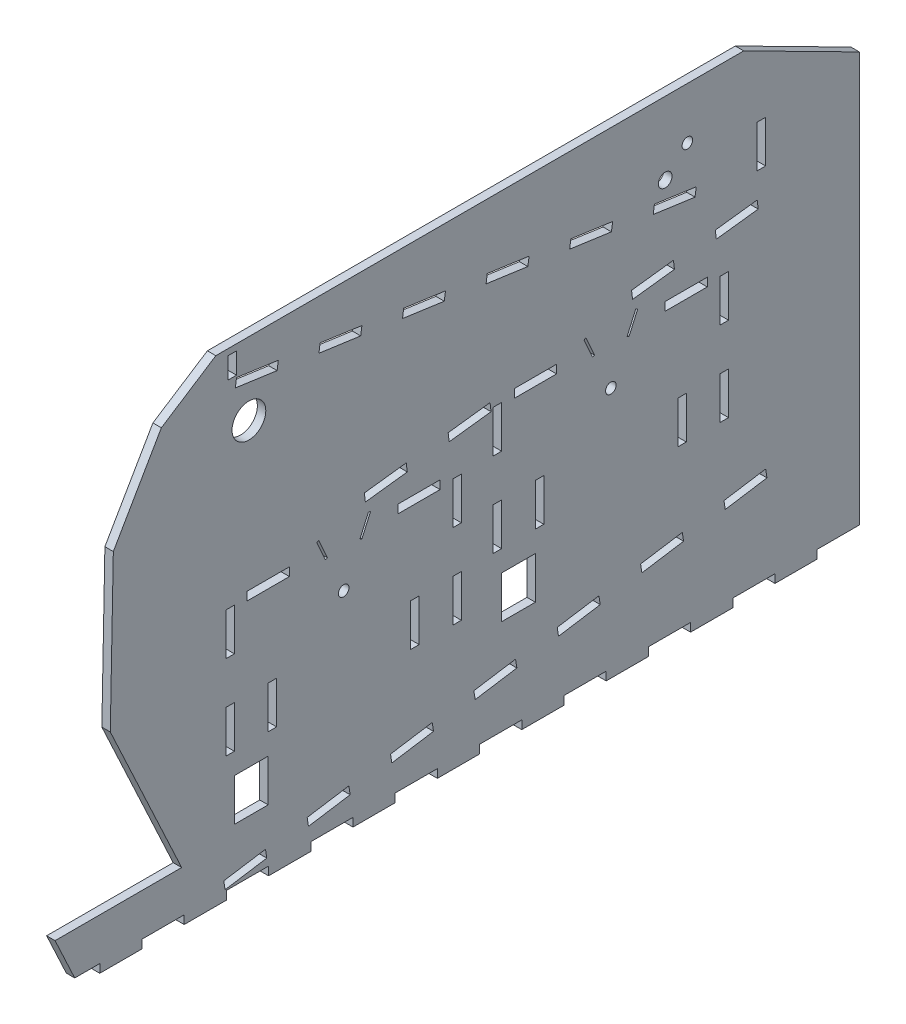
SolidWorks part; units mm, degrees
ref_plane "Спереди" through (0, 0, 0) normal (0, 0, 1) x (1, 0, 0)
ref_plane "Сверху" through (0, 0, 0) normal (0, 1, 0) x (1, 0, 0)
ref_plane "Справа" through (0, 0, 0) normal (1, 0, 0) x (0, 0, -1)
sketch "Эскиз1" plane through (0, 0, 0) normal (1, 0, 0) x (0, 0, -1)
  line L0 (0, 0) -> (-31.7705, 0) construction
  line L1 (0, 0) -> (-25.7029, 18.6742) construction
  line L2 (0, 0) -> (-25.7029, 18.6742) construction
  line L3 (0, 0) -> (-9.8176, 30.2156) construction
  line L4 (0, 0) -> (-9.8176, 30.2156) construction
  line L5 (0, 0) -> (9.8176, 30.2156) construction
  line L6 (0, 0) -> (9.8176, 30.2156) construction
  line L7 (0, 0) -> (25.7029, 18.6742) construction
  line L8 (0, 0) -> (25.7029, 18.6742) construction
  line L9 (0, 0) -> (31.7705, 0) construction
  line L10 (-31.7705, 0) -> (-31.7705, -31.7705) construction
  line L11 (-25.7029, 18.6742) -> (-51.7705, 18.6742) construction
  line L12 (-51.7705, 18.6742) -> (-51.7705, -31.7705) construction
  line L13 (0, 0) -> (0, -37.2268) construction
  line L14 (25.7029, 18.6742) -> (51.7705, 18.6742) construction
  line L15 (51.7705, 18.6742) -> (51.7705, -31.7705) construction
  line L16 (31.7705, 0) -> (31.7705, -31.7705) construction
  line L17 (10.3051, 31.2454) -> (28.3345, 31.2454) construction
  line L18 (9.8176, 35.2156) -> (10.3051, 31.2454) construction
  line L19 (9.8176, 35.2156) -> (69.3704, 42.5277) construction
  line L20 (10.3051, 31.2454) -> (69.8579, 38.5575) construction
  line L21 (25.7029, 18.6742) -> (25.7029, 22.6742) construction
  line L22 (25.7029, 22.6742) -> (55.7705, 22.6742) construction
  line L23 (55.7705, 22.6742) -> (55.7705, -31.7705) construction
  line L24 (55.7705, -31.7705) -> (51.7705, -31.7705) construction
  line L25 (31.7705, 0) -> (35.7705, 0) construction
  line L26 (35.7705, 0) -> (35.7705, -31.7705) construction
  line L27 (35.7705, -31.7705) -> (31.7705, -31.7705) construction
  line L28 (-31.7705, 0) -> (-35.7705, 0) construction
  line L29 (-35.7705, 0) -> (-35.7705, -31.7705) construction
  line L30 (-35.7705, -31.7705) -> (-31.7705, -31.7705) construction
  line L31 (-31.7705, -31.7705) -> (-32.0988, -31.7383) construction
  line L32 (-25.7029, 18.6742) -> (-25.7029, 22.6742) construction
  line L33 (-25.7029, 22.6742) -> (-55.7705, 22.6742) construction
  line L34 (-55.7705, 22.6742) -> (-55.7705, -31.7705) construction
  line L35 (-55.7705, -31.7705) -> (-51.7705, -31.7705) construction
  line L36 (69.3704, 42.5277) -> (69.8579, 38.5575) construction
  line L37 (9.8176, 30.2156) -> (9.8176, 40.2156)
  line L38 (51.7705, 18.6742) -> (55.7705, 18.6742) construction
  line L39 (126.6284, 19.8535) -> (94.8579, 19.8535) construction
  line L40 (126.6284, 19.8535) -> (100.9255, 38.5277) construction
  line L41 (126.6284, 19.8535) -> (100.9255, 38.5277) construction
  line L42 (126.6284, 19.8535) -> (116.8108, 50.069) construction
  line L43 (126.6284, 19.8535) -> (116.8108, 50.069) construction
  line L44 (126.6284, 19.8535) -> (136.446, 50.069) construction
  line L45 (199.9988, -50.0348) -> (180.2402, -53.1327)
  line L46 (126.6284, 19.8535) -> (136.446, 50.069) construction
  line L47 (126.6284, 19.8535) -> (152.3313, 38.5277) construction
  line L48 (126.6284, 19.8535) -> (152.3313, 38.5277) construction
  line L49 (126.6284, 19.8535) -> (158.3989, 19.8535) construction
  line L50 (94.8579, 19.8535) -> (94.8579, -11.917) construction
  line L51 (100.9255, 38.5277) -> (74.8579, 38.5277) construction
  line L52 (74.8579, 38.5277) -> (74.8579, -11.917) construction
  line L53 (126.6284, 19.8535) -> (126.6284, -17.4484) construction
  line L54 (152.3313, 38.5277) -> (178.3989, 38.5277) construction
  line L55 (178.3989, 38.5277) -> (178.3989, -11.917) construction
  line L56 (158.3989, 19.8535) -> (158.3989, -11.917) construction
  line L57 (136.9335, 51.0988) -> (174.1594, 51.0988) construction
  line L58 (136.446, 55.069) -> (136.9335, 51.0988) construction
  line L59 (136.446, 55.069) -> (195.9988, 62.3812) construction
  line L60 (136.9335, 51.0988) -> (196.4863, 58.411) construction
  line L61 (152.3313, 38.5277) -> (152.3313, 42.5277) construction
  line L62 (152.3313, 42.5277) -> (182.3989, 42.5277) construction
  line L63 (182.3989, 42.5277) -> (182.3989, -11.917) construction
  line L64 (182.3989, -11.917) -> (178.3989, -11.917) construction
  line L65 (158.3989, 19.8535) -> (162.3989, 19.8535) construction
  line L66 (69.3704, 42.5277) -> (69.8579, 38.5575)
  line L67 (69.3704, 42.5277) -> (49.5195, 40.0903)
  line L68 (69.8579, 38.5575) -> (50.007, 36.1201)
  line L69 (49.5195, 40.0903) -> (50.007, 36.1201)
  line L70 (29.6686, 37.6529) -> (9.8176, 35.2156)
  line L71 (9.8176, 35.2156) -> (10.3051, 31.2454)
  line L72 (30.156, 33.6828) -> (10.3051, 31.2454)
  line L73 (29.6686, 37.6529) -> (30.156, 33.6828)
  line L74 (162.3989, 19.8535) -> (162.3989, -11.917) construction
  line L75 (25.7029, 18.6742) -> (45.7029, 18.6742)
  line L76 (25.7029, 18.6742) -> (25.7029, 22.6742)
  line L77 (25.7029, 22.6742) -> (45.7029, 22.6742)
  line L78 (45.7029, 18.6742) -> (45.7029, 22.6742)
  line L79 (51.7705, 20) -> (55.7705, 20)
  line L80 (51.7705, 20) -> (51.7705, 0)
  line L81 (51.7705, 0) -> (55.7705, 0)
  line L82 (55.7705, 20) -> (55.7705, 0)
  line L83 (-31.7705, -20) -> (-35.7705, -20)
  line L84 (-31.7705, -20) -> (-31.7705, -40)
  line L85 (-31.7705, -40) -> (-35.7705, -40)
  line L86 (-25.7029, 18.6742) -> (-45.7029, 18.6742)
  line L87 (-25.7029, 18.6742) -> (-25.7029, 22.6742)
  line L88 (-25.7029, 22.6742) -> (-45.7029, 22.6742)
  line L89 (-45.7029, 18.6742) -> (-45.7029, 22.6742)
  line L90 (-35.7705, -20) -> (-35.7705, -40)
  line L91 (31.7705, -20) -> (35.7705, -20)
  line L92 (31.7705, -20) -> (31.7705, -40)
  line L93 (31.7705, -40) -> (35.7705, -40)
  line L94 (-55.7705, 20) -> (-51.7705, 20)
  line L95 (-55.7705, 20) -> (-55.7705, 0)
  line L96 (-55.7705, 0) -> (-51.7705, 0)
  line L97 (-51.7705, 20) -> (-51.7705, 0)
  line L98 (162.3989, -11.917) -> (158.3989, -11.917) construction
  line L99 (94.8579, 19.8535) -> (90.8579, 19.8535) construction
  line L100 (90.8579, 19.8535) -> (90.8579, -11.917) construction
  line L101 (90.8579, -11.917) -> (94.8579, -11.917) construction
  line L102 (179.9988, 80.4295) -> (130.5186, 80.4295) construction
  line L103 (100.9255, 38.5277) -> (100.9255, 42.5277) construction
  line L104 (100.9255, 42.5277) -> (70.8579, 42.5277) construction
  line L105 (70.8579, 42.5277) -> (70.8579, -11.917) construction
  line L106 (70.8579, -11.917) -> (74.8579, -11.917) construction
  line L107 (195.9988, 62.3812) -> (196.4863, 58.411) construction
  line L108 (136.446, 50.069) -> (136.446, 60.069)
  line L109 (178.3989, 38.5277) -> (182.3989, 38.5277) construction
  line L110 (179.9988, 80.4295) -> (179.4421, 76.4684) construction
  line L111 (195.9988, 62.3812) -> (196.4863, 58.411)
  line L112 (195.9988, 62.3812) -> (176.1479, 59.9438)
  line L113 (35.7705, -20) -> (35.7705, -40)
  line L114 (196.4863, 58.411) -> (176.6353, 55.9736)
  line L115 (176.1479, 59.9438) -> (176.6353, 55.9736)
  line L116 (156.2969, 57.5064) -> (136.446, 55.069)
  line L117 (136.446, 55.069) -> (136.9335, 51.0988)
  line L118 (156.7844, 53.5362) -> (136.9335, 51.0988)
  line L119 (156.2969, 57.5064) -> (156.7844, 53.5362)
  line L120 (152.3313, 38.5277) -> (172.3313, 38.5277)
  line L121 (152.3313, 38.5277) -> (152.3313, 42.5277)
  line L122 (152.3313, 42.5277) -> (172.3313, 42.5277)
  line L123 (172.3313, 38.5277) -> (172.3313, 42.5277)
  line L124 (178.3989, 19.8535) -> (182.3989, 19.8535)
  line L125 (178.3989, 19.8535) -> (178.3989, 39.8535)
  line L126 (178.3989, 39.8535) -> (182.3989, 39.8535)
  line L127 (182.3989, 19.8535) -> (182.3989, 39.8535)
  line L128 (94.8579, -0.1465) -> (90.8579, -0.1465)
  line L129 (94.8579, -0.1465) -> (94.8579, -20.1465)
  line L130 (94.8579, -20.1465) -> (90.8579, -20.1465)
  line L131 (100.9255, 38.5277) -> (80.9255, 38.5277)
  line L132 (100.9255, 38.5277) -> (100.9255, 42.5277)
  line L133 (100.9255, 42.5277) -> (80.9255, 42.5277)
  line L134 (80.9255, 38.5277) -> (80.9255, 42.5277)
  line L135 (90.8579, -0.1465) -> (90.8579, -20.1465)
  line L136 (158.3989, -0.1465) -> (162.3989, -0.1465)
  line L137 (158.3989, -0.1465) -> (158.3989, -20.1465)
  line L138 (158.3989, -20.1465) -> (162.3989, -20.1465)
  line L139 (70.8579, 39.8535) -> (74.8579, 39.8535)
  line L140 (70.8579, 39.8535) -> (70.8579, 19.8535)
  line L141 (70.8579, 19.8535) -> (74.8579, 19.8535)
  line L142 (74.8579, 39.8535) -> (74.8579, 19.8535)
  line L143 (162.3989, -0.1465) -> (162.3989, -20.1465)
  line L144 (179.9988, 80.4295) -> (-50.7705, 112.862) construction
  line L145 (-50.7705, 112.862) -> (-50.7705, 126.7706) construction
  line L146 (195.9988, 62.3812) -> (195.9988, 94.3381) construction
  line L147 (-76.7705, -75.2294) -> (-128.8786, 36.5168)
  line L148 (195.9988, 94.3381) -> (-34.7705, 126.7706) construction
  line L149 (-34.7705, 126.7706) -> (244.4209, 126.7706)
  line L150 (-51.7705, -40) -> (-51.7705, -50) construction
  line L151 (162.8814, 102.3387) -> (147.4568, 90.7154) construction
  line L152 (162.8814, 102.3387) -> (174.5046, 86.9141) construction
  line L153 (162.8814, 102.3387) -> (182.0071, 99.6508) construction
  line L154 (162.8814, 102.3387) -> (160.1934, 83.213) construction
  line L155 (-55.7705, -20) -> (-51.7705, -20)
  line L156 (-55.7705, -20) -> (-55.7705, -40)
  line L157 (-55.7705, -40) -> (-51.7705, -40)
  line L158 (-51.7705, -20) -> (-51.7705, -40)
  line L159 (74.8579, -20.1465) -> (74.8579, -50.1465) construction
  line L160 (-51.7705, -50) -> (-35.7705, -50)
  line L161 (-51.7705, -50) -> (-51.7705, -70)
  line L162 (-51.7705, -70) -> (-35.7705, -70)
  line L163 (-35.7705, -50) -> (-35.7705, -70)
  line L164 (70.8579, -0.1465) -> (74.8579, -0.1465)
  line L165 (70.8579, -0.1465) -> (70.8579, -20.1465)
  line L166 (70.8579, -20.1465) -> (74.8579, -20.1465)
  line L167 (74.8579, -0.1465) -> (74.8579, -20.1465)
  line L168 (-132.357, -75.2294) -> (-123.0308, -95.2294) construction
  line L169 (74.8579, -50.1465) -> (90.8579, -50.1465)
  line L170 (74.8579, -50.1465) -> (74.8579, -30.1465)
  line L171 (74.8579, -30.1465) -> (90.8579, -30.1465)
  line L172 (90.8579, -50.1465) -> (90.8579, -30.1465)
  line L173 (51.7705, -20) -> (55.7705, -20)
  line L174 (51.7705, -20) -> (51.7705, -40)
  line L175 (51.7705, -40) -> (55.7705, -40)
  line L176 (55.7705, -20) -> (55.7705, -40)
  line L177 (178.3989, -0.1465) -> (182.3989, -0.1465)
  line L178 (178.3989, -0.1465) -> (178.3989, -20.1465)
  line L179 (178.3989, -20.1465) -> (182.3989, -20.1465)
  line L180 (182.3989, -0.1465) -> (182.3989, -20.1465)
  line L181 (-88.2588, -95.2294) -> (199.9988, -50.0348) construction
  line L182 (-123.0308, -95.2294) -> (-88.2588, -95.2294) construction
  line L183 (-132.357, -75.2294) -> (-136.7705, -75.2294) construction
  line L184 (-76.7705, -75.2294) -> (-136.7705, -75.2294)
  line L185 (-136.7705, -75.2294) -> (-125.5791, -99.2294)
  line L186 (-125.5791, -99.2294) -> (244.4209, -99.2294)
  line L187 (244.4209, -99.2294) -> (244.4209, 126.7706)
  line L188 (-128.8786, 36.5168) -> (-76.7705, 126.7706)
  line L189 (-76.7705, 126.7706) -> (-34.7705, 126.7706)
  line L190 (-50.7705, 112.862) -> (-30.9651, 110.0786)
  line L191 (204.4209, -99.2294) -> (184.4209, -99.2294)
  line L192 (-50.7705, 113.862) -> (-54.7705, 113.862)
  line L193 (-50.7705, 113.862) -> (-50.7705, 123.862)
  line L194 (-50.7705, 123.862) -> (-54.7705, 123.862)
  line L195 (-50.7705, 112.862) -> (-51.3272, 108.9009)
  line L196 (-30.9651, 110.0786) -> (-31.5218, 106.1175)
  line L197 (-51.3272, 108.9009) -> (-31.5218, 106.1175)
  line L198 (-11.1598, 107.2951) -> (-11.7165, 103.334)
  line L199 (-11.7165, 103.334) -> (8.0889, 100.5506)
  line L200 (8.6456, 104.5116) -> (8.0889, 100.5506)
  line L201 (-11.1598, 107.2951) -> (8.6456, 104.5116)
  line L202 (28.4509, 101.7282) -> (27.8942, 97.7671)
  line L203 (27.8942, 97.7671) -> (47.6996, 94.9836)
  line L204 (48.2563, 98.9447) -> (47.6996, 94.9836)
  line L205 (28.4509, 101.7282) -> (48.2563, 98.9447)
  line L206 (68.0617, 96.1612) -> (67.505, 92.2002)
  line L207 (67.505, 92.2002) -> (87.3103, 89.4167)
  line L208 (87.867, 93.3778) -> (87.3103, 89.4167)
  line L209 (68.0617, 96.1612) -> (87.867, 93.3778)
  line L210 (107.6724, 90.5943) -> (107.1157, 86.6332)
  line L211 (107.1157, 86.6332) -> (126.9211, 83.8498)
  line L212 (127.4777, 87.8109) -> (126.9211, 83.8498)
  line L213 (107.6724, 90.5943) -> (127.4777, 87.8109)
  line L214 (147.2831, 85.0274) -> (146.7264, 81.0663)
  line L215 (146.7264, 81.0663) -> (166.5318, 78.2829)
  line L216 (167.0885, 82.2439) -> (166.5318, 78.2829)
  line L217 (147.2831, 85.0274) -> (167.0885, 82.2439)
  line L218 (179.9988, 80.4295) -> (175.1542, 81.1104) construction
  line L219 (179.4421, 76.4684) -> (174.5975, 77.1493) construction
  line L220 (175.1542, 81.1104) -> (174.5975, 77.1493) construction
  line L221 (195.9988, 94.3381) -> (199.9988, 94.3381)
  line L222 (195.9988, 94.3381) -> (195.9988, 74.3381)
  line L223 (195.9988, 74.3381) -> (199.9988, 74.3381)
  line L224 (199.9988, 94.3381) -> (199.9988, 74.3381)
  line L225 (199.9988, -50.0348) -> (200.6184, -53.9866)
  line L226 (180.2402, -53.1327) -> (180.8597, -57.0844)
  line L227 (200.6184, -53.9866) -> (180.8597, -57.0844)
  line L228 (160.4912, -56.2922) -> (140.7326, -59.3901)
  line L229 (160.4912, -56.2922) -> (161.1108, -60.2439)
  line L230 (140.7326, -59.3901) -> (141.3522, -63.3418)
  line L231 (161.1108, -60.2439) -> (141.3522, -63.3418)
  line L232 (120.9837, -62.5496) -> (101.2251, -65.6475)
  line L233 (120.9837, -62.5496) -> (121.6033, -66.5013)
  line L234 (101.2251, -65.6475) -> (101.8447, -69.5992)
  line L235 (121.6033, -66.5013) -> (101.8447, -69.5992)
  line L236 (81.4762, -68.807) -> (61.7176, -71.9048)
  line L237 (81.4762, -68.807) -> (82.0958, -72.7587)
  line L238 (61.7176, -71.9048) -> (62.3371, -75.8566)
  line L239 (82.0958, -72.7587) -> (62.3371, -75.8566)
  line L240 (41.9686, -75.0643) -> (22.21, -78.1622)
  line L241 (41.9686, -75.0643) -> (42.5882, -79.0161)
  line L242 (22.21, -78.1622) -> (22.8296, -82.1139)
  line L243 (42.5882, -79.0161) -> (22.8296, -82.1139)
  line L244 (2.4611, -81.3217) -> (-17.2975, -84.4196)
  line L245 (2.4611, -81.3217) -> (3.0807, -85.2735)
  line L246 (-17.2975, -84.4196) -> (-16.6779, -88.3713)
  line L247 (3.0807, -85.2735) -> (-16.6779, -88.3713)
  line L248 (-54.7705, 113.862) -> (-54.7705, 123.862)
  line L249 (244.4209, -99.2294) -> (224.4209, -99.2294)
  line L250 (244.4209, -99.2294) -> (244.4209, -95.2294)
  line L251 (244.4209, -95.2294) -> (224.4209, -95.2294)
  line L252 (224.4209, -99.2294) -> (224.4209, -95.2294)
  line L253 (204.4209, -99.2294) -> (204.4209, -95.2294)
  line L254 (204.4209, -95.2294) -> (184.4209, -95.2294)
  line L255 (184.4209, -99.2294) -> (184.4209, -95.2294)
  line L256 (164.4209, -99.2294) -> (144.4209, -99.2294)
  line L257 (164.4209, -99.2294) -> (164.4209, -95.2294)
  line L258 (164.4209, -95.2294) -> (144.4209, -95.2294)
  line L259 (144.4209, -99.2294) -> (144.4209, -95.2294)
  line L260 (124.4209, -99.2294) -> (104.4209, -99.2294)
  line L261 (124.4209, -99.2294) -> (124.4209, -95.2294)
  line L262 (124.4209, -95.2294) -> (104.4209, -95.2294)
  line L263 (104.4209, -99.2294) -> (104.4209, -95.2294)
  line L264 (84.4209, -99.2294) -> (64.4209, -99.2294)
  line L265 (84.4209, -99.2294) -> (84.4209, -95.2294)
  line L266 (84.4209, -95.2294) -> (64.4209, -95.2294)
  line L267 (64.4209, -99.2294) -> (64.4209, -95.2294)
  line L268 (44.4209, -99.2294) -> (24.4209, -99.2294)
  line L269 (44.4209, -99.2294) -> (44.4209, -95.2294)
  line L270 (44.4209, -95.2294) -> (24.4209, -95.2294)
  line L271 (24.4209, -99.2294) -> (24.4209, -95.2294)
  line L272 (4.4209, -99.2294) -> (-15.5791, -99.2294)
  line L273 (4.4209, -99.2294) -> (4.4209, -95.2294)
  line L274 (4.4209, -95.2294) -> (-15.5791, -95.2294)
  line L275 (-15.5791, -99.2294) -> (-15.5791, -95.2294)
  line L276 (-35.5791, -99.2294) -> (-55.5791, -99.2294)
  line L277 (-35.5791, -99.2294) -> (-35.5791, -95.2294)
  line L278 (-35.5791, -95.2294) -> (-55.5791, -95.2294)
  line L279 (-55.5791, -99.2294) -> (-55.5791, -95.2294)
  line L280 (-75.5791, -99.2294) -> (-95.5791, -99.2294)
  line L281 (-75.5791, -99.2294) -> (-75.5791, -95.2294)
  line L282 (-75.5791, -95.2294) -> (-95.5791, -95.2294)
  line L283 (-95.5791, -99.2294) -> (-95.5791, -95.2294)
  line L284 (-115.5791, -99.2294) -> (-135.5791, -99.2294)
  line L285 (-115.5791, -99.2294) -> (-115.5791, -95.2294)
  line L286 (-115.5791, -95.2294) -> (-135.5791, -95.2294)
  line L287 (-135.5791, -99.2294) -> (-135.5791, -95.2294)
  line L288 (-110.6007, -2.6803) -> (-109.1606, 70.6694)
  line L289 (-37.0464, -87.5791) -> (-56.805, -90.677)
  line L290 (-37.0464, -87.5791) -> (-36.4268, -91.5308)
  line L291 (-56.805, -90.677) -> (-56.1855, -94.6287)
  line L292 (-36.4268, -91.5308) -> (-56.1855, -94.6287)
  line L293 (-86.4077, 110.0786) -> (-60.5791, 126.7706)
  line L294 (189.6222, 126.7706) -> (244.4209, 98.9447)
  line L295 (-12.7089, 26.0861) -> (-8.6415, 16.9506)
  line L296 (-12.7089, 26.0861) -> (-11.7954, 26.4928)
  line L297 (-8.6415, 16.9506) -> (-7.728, 17.3574)
  line L298 (-11.7954, 26.4928) -> (-7.728, 17.3574)
  line L299 (8.6415, 16.9506) -> (7.728, 17.3574)
  line L300 (11.7954, 26.4928) -> (7.728, 17.3574)
  line L301 (12.7089, 26.0861) -> (8.6415, 16.9506)
  line L302 (12.7089, 26.0861) -> (11.7954, 26.4928)
  line L303 (114.833, 46.3463) -> (118.9004, 37.2108)
  line L304 (114.833, 46.3463) -> (113.9195, 45.9396)
  line L305 (118.9004, 37.2108) -> (117.9868, 36.8041)
  line L306 (113.9195, 45.9396) -> (117.9868, 36.8041)
  line L307 (134.3564, 37.2108) -> (135.2699, 36.8041)
  line L308 (139.3373, 45.9396) -> (135.2699, 36.8041)
  line L309 (138.4237, 46.3463) -> (134.3564, 37.2108)
  line L310 (138.4237, 46.3463) -> (139.3373, 45.9396)
  line L311 (161.3068, 91.1351) -> (116.07, 97.4927) construction
  circle A0 centre (0, 0) radius 31.7705 construction
  circle A1 centre (-23.0826, 7.5) radius 7.5 construction
  circle A2 centre (-14.2658, 19.6353) radius 7.5 construction
  circle A3 centre (0, 24.2705) radius 7.5 construction
  circle A4 centre (14.2658, 19.6353) radius 7.5 construction
  circle A5 centre (23.0826, 7.5) radius 7.5 construction
  circle A6 centre (0, 0) radius 2.5
  circle A7 centre (126.6284, 19.8535) radius 31.7705 construction
  circle A8 centre (103.5458, 27.3535) radius 7.5 construction
  circle A9 centre (112.3625, 39.4887) radius 7.5 construction
  circle A10 centre (126.6284, 44.124) radius 7.5 construction
  circle A11 centre (140.8942, 39.4887) radius 7.5 construction
  circle A12 centre (149.711, 27.3535) radius 7.5 construction
  circle A13 centre (126.6284, 19.8535) radius 2.5
  circle A14 centre (162.8814, 102.3387) radius 19.3137 construction
  circle A15 centre (161.3068, 91.1351) radius 8 construction
  arc A16 (177.7354, 100.2511) -> (170.529, 120.0738) centre (158.1612, 104.3563) ccw construction
  circle A17 centre (162.8814, 102.3387) radius 2.5
  circle A18 centre (169.6901, 93.3032) radius 8 construction
  circle A19 centre (152.3944, 92.3877) radius 3.25
  point P6 (0, 31.7705)
  point P55 (126.6284, 51.624)
  point P192 (-35.7705, -87)
  point P194 (90.8579, -67.1465)
  dimension "D1" = 15
  dimension "D20" = 5
  dimension "D7" = 15
  dimension "D35" = 5
  dimension "D50" = 20
  dimension "D51" = 5
  dimension "D52" = 16
  dimension "D85" = 6.5
  dimension "D2" = 36
  dimension "D3" = 16
  dimension "D4" = 16
  dimension "D5" = 60
  dimension "D8" = 36
  dimension "D9" = 16
  dimension "D10" = 16
  dimension "D11" = 4
  dimension "D12" = 60
  dimension "D13" = 20
  dimension "D14" = 20
  dimension "D15" = 20
  dimension "D16" = 20
  dimension "D17" = 20
  dimension "D18" = 30
  dimension "D19" = 20
  dimension "D21" = 4
  dimension "D22" = 20
  dimension "D23" = 20
  dimension "D24" = 20
  dimension "D25" = 4
  dimension "D26" = 20
  dimension "D27" = 7
  dimension "D28" = 5
  dimension "D29" = 20
  dimension "D30" = 20
  dimension "D31" = 17
  dimension "D32" = 20
  dimension "D33" = 30
  dimension "D34" = 20
  dimension "D36" = 20
  dimension "D37" = 20
  dimension "D38" = 4
  dimension "D39" = 20
  dimension "D40" = 7
  dimension "D41" = 5
  dimension "D42" = 16
  dimension "D43" = 16
  dimension "D44" = 26
  dimension "D45" = 4
  dimension "D46" = 45
  dimension "D47" = 16
  dimension "D48" = 4
  dimension "D49" = 15
  dimension "D53" = 20
  dimension "D54" = 20
  dimension "D55" = 20
  dimension "D56" = 17
  dimension "D57" = 125
  dimension "D58" = 21
  dimension "D59" = 60
  dimension "D60" = 226
  dimension "D61" = 8
  dimension "D62" = 16
  dimension "D63" = 120
  dimension "D64" = 370
  dimension "D65" = 10
  dimension "D66" = 1
  dimension "D67" = 20
  dimension "D69" = 20
  dimension "D70" = 20
  dimension "D71" = 4
  dimension "D73" = 4
  dimension "D74" = 4
  dimension "D76" = 1
  dimension "D75" = 20
  dimension "D77" = 1
  dimension "D78" = 19
  dimension "D79" = 10
  dimension "D80" = 6
  dimension "D81" = 19
  dimension "D82" = 1
  dimension "D83" = 10
  dimension "D84" = 6
  dimension "D86" = 9
  dimension "D68" = 6
  dimension "D72" = 7
extrude "Бобышка-Вытянуть12" add sketch "Эскиз1" along normal blind 4 contours L189 L188 L147 L184 L185 L186 L187 L149 A17 A13 A6 L197 L195 L190 L196 L172 L169 L170 L171 L135 L128 L129 L130 L127 L124 L125 L126 L123 L120 L121 L122 L115 L112 L111 L114 L90 L83 L84 L85 L78
sketch "Эскиз2" plane through (4, 0, 0) normal (1, 0, 0) x (0, 0, -1)
  line L0 (-136.7705, -75.2294) -> (-127.4444, -95.2294)
  line L1 (-127.4444, -95.2294) -> (244.4209, -95.2294)
  line L2 (244.4209, -95.2294) -> (273.2182, 68.0882)
  line L3 (-136.7705, -75.2294) -> (-76.7705, -75.2294)
  line L4 (-76.7705, -75.2294) -> (-117.8785, 12.9271)
  line L5 (-76.7705, -75.2294) -> (-110.6007, -2.6803) construction
  line L6 (-115.8644, 59.058) -> (-83.41, 115.2706)
  line L7 (-109.1606, 70.6694) -> (-86.4077, 110.0786) construction
  line L8 (-63.4915, 126.7706) -> (223.9778, 126.7706)
  line L9 (-60.5791, 126.7706) -> (189.6222, 126.7706) construction
  line L10 (-85.2229, -57.1032) -> (-88.8481, -58.7937)
  line L11 (-85.2229, -57.1032) -> (-89.4491, -48.0402)
  line L12 (-88.8481, -58.7937) -> (-93.0743, -49.7306)
  line L13 (-89.4491, -48.0402) -> (-93.0743, -49.7306)
  line L14 (-93.6752, -38.9771) -> (-97.3005, -40.6676)
  line L15 (-93.6752, -38.9771) -> (-97.9014, -29.914)
  line L16 (-97.3005, -40.6676) -> (-101.5267, -31.6045)
  line L17 (-97.9014, -29.914) -> (-101.5267, -31.6045)
  line L18 (-102.1276, -20.8509) -> (-105.7528, -22.5414)
  line L19 (-102.1276, -20.8509) -> (-106.3538, -11.7879)
  line L20 (-105.7528, -22.5414) -> (-109.979, -13.4783)
  line L21 (-106.3538, -11.7879) -> (-109.979, -13.4783)
  line L22 (-110.58, -2.7248) -> (-114.2052, -4.4152)
  line L23 (-110.58, -2.7248) -> (-114.8062, 6.3383)
  line L24 (-114.2052, -4.4152) -> (-118.4314, 4.6478)
  line L25 (-114.8062, 6.3383) -> (-118.4314, 4.6478)
  line L26 (-110.8644, 67.7182) -> (-105.8644, 76.3785)
  line L27 (-110.8644, 67.7182) -> (-114.3285, 69.7182)
  line L28 (-105.8644, 76.3785) -> (-109.3285, 78.3785)
  line L29 (-114.3285, 69.7182) -> (-109.3285, 78.3785)
  line L30 (-100.8644, 85.0387) -> (-95.8644, 93.699)
  line L31 (-100.8644, 85.0387) -> (-104.3285, 87.0387)
  line L32 (-95.8644, 93.699) -> (-99.3285, 95.699)
  line L33 (-104.3285, 87.0387) -> (-99.3285, 95.699)
  line L34 (-90.8644, 102.3592) -> (-85.8644, 111.0195)
  line L35 (-90.8644, 102.3592) -> (-94.3285, 104.3592)
  line L36 (-85.8644, 111.0195) -> (-89.3285, 113.0195)
  line L37 (-94.3285, 104.3592) -> (-89.3285, 113.0195)
  line L38 (-33.4915, 126.7706) -> (-23.4915, 126.7706)
  line L39 (-53.4915, 126.7706) -> (-43.4915, 126.7706)
  line L40 (-53.4915, 126.7706) -> (-53.4915, 130.7706)
  line L41 (-53.4915, 130.7706) -> (-43.4915, 130.7706)
  line L42 (-43.4915, 126.7706) -> (-43.4915, 130.7706)
  line L43 (-33.4915, 126.7706) -> (-33.4915, 130.7706)
  line L44 (-33.4915, 130.7706) -> (-23.4915, 130.7706)
  line L45 (-23.4915, 126.7706) -> (-23.4915, 130.7706)
  line L46 (-13.4915, 126.7706) -> (-3.4915, 126.7706)
  line L47 (-13.4915, 126.7706) -> (-13.4915, 130.7706)
  line L48 (-13.4915, 130.7706) -> (-3.4915, 130.7706)
  line L49 (-3.4915, 126.7706) -> (-3.4915, 130.7706)
  line L50 (6.5085, 126.7706) -> (16.5085, 126.7706)
  line L51 (6.5085, 126.7706) -> (6.5085, 130.7706)
  line L52 (6.5085, 130.7706) -> (16.5085, 130.7706)
  line L53 (16.5085, 126.7706) -> (16.5085, 130.7706)
  line L54 (26.5085, 126.7706) -> (36.5085, 126.7706)
  line L55 (26.5085, 126.7706) -> (26.5085, 130.7706)
  line L56 (26.5085, 130.7706) -> (36.5085, 130.7706)
  line L57 (36.5085, 126.7706) -> (36.5085, 130.7706)
  line L58 (46.5085, 126.7706) -> (56.5085, 126.7706)
  line L59 (46.5085, 126.7706) -> (46.5085, 130.7706)
  line L60 (46.5085, 130.7706) -> (56.5085, 130.7706)
  line L61 (56.5085, 126.7706) -> (56.5085, 130.7706)
  line L62 (66.5085, 126.7706) -> (76.5085, 126.7706)
  line L63 (66.5085, 126.7706) -> (66.5085, 130.7706)
  line L64 (66.5085, 130.7706) -> (76.5085, 130.7706)
  line L65 (76.5085, 126.7706) -> (76.5085, 130.7706)
  line L66 (86.5085, 126.7706) -> (96.5085, 126.7706)
  line L67 (86.5085, 126.7706) -> (86.5085, 130.7706)
  line L68 (86.5085, 130.7706) -> (96.5085, 130.7706)
  line L69 (96.5085, 126.7706) -> (96.5085, 130.7706)
  line L70 (106.5085, 126.7706) -> (116.5085, 126.7706)
  line L71 (106.5085, 126.7706) -> (106.5085, 130.7706)
  line L72 (106.5085, 130.7706) -> (116.5085, 130.7706)
  line L73 (116.5085, 126.7706) -> (116.5085, 130.7706)
  line L74 (126.5085, 126.7706) -> (136.5085, 126.7706)
  line L75 (126.5085, 126.7706) -> (126.5085, 130.7706)
  line L76 (126.5085, 130.7706) -> (136.5085, 130.7706)
  line L77 (136.5085, 126.7706) -> (136.5085, 130.7706)
  line L78 (146.5085, 126.7706) -> (156.5085, 126.7706)
  line L79 (146.5085, 126.7706) -> (146.5085, 130.7706)
  line L80 (146.5085, 130.7706) -> (156.5085, 130.7706)
  line L81 (156.5085, 126.7706) -> (156.5085, 130.7706)
  line L82 (166.5085, 126.7706) -> (176.5085, 126.7706)
  line L83 (166.5085, 126.7706) -> (166.5085, 130.7706)
  line L84 (166.5085, 130.7706) -> (176.5085, 130.7706)
  line L85 (176.5085, 126.7706) -> (176.5085, 130.7706)
  line L86 (186.5085, 126.7706) -> (196.5085, 126.7706)
  line L87 (186.5085, 126.7706) -> (186.5085, 130.7706)
  line L88 (186.5085, 130.7706) -> (196.5085, 130.7706)
  line L89 (196.5085, 126.7706) -> (196.5085, 130.7706)
  line L90 (271.4817, 58.2401) -> (269.7452, 48.392)
  line L91 (271.4817, 58.2401) -> (275.4209, 57.5455)
  line L92 (269.7452, 48.392) -> (273.6844, 47.6974)
  line L93 (275.4209, 57.5455) -> (273.6844, 47.6974)
  line L94 (268.0087, 38.544) -> (266.2722, 28.6959)
  line L95 (268.0087, 38.544) -> (271.948, 37.8494)
  line L96 (266.2722, 28.6959) -> (270.2115, 28.0013)
  line L97 (271.948, 37.8494) -> (270.2115, 28.0013)
  line L98 (264.5358, 18.8478) -> (262.7993, 8.9997)
  line L99 (264.5358, 18.8478) -> (268.475, 18.1532)
  line L100 (262.7993, 8.9997) -> (266.7385, 8.3051)
  line L101 (268.475, 18.1532) -> (266.7385, 8.3051)
  line L102 (261.0628, -0.8483) -> (259.3263, -10.6964)
  line L103 (261.0628, -0.8483) -> (265.002, -1.5429)
  line L104 (259.3263, -10.6964) -> (263.2655, -11.391)
  line L105 (265.002, -1.5429) -> (263.2655, -11.391)
  line L106 (257.5898, -20.5445) -> (255.8534, -30.3926)
  line L107 (257.5898, -20.5445) -> (261.5291, -21.2391)
  line L108 (255.8534, -30.3926) -> (259.7926, -31.0872)
  line L109 (261.5291, -21.2391) -> (259.7926, -31.0872)
  line L110 (254.1169, -40.2407) -> (252.3804, -50.0887)
  line L111 (254.1169, -40.2407) -> (258.0561, -40.9352)
  line L112 (252.3804, -50.0887) -> (256.3196, -50.7833)
  line L113 (258.0561, -40.9352) -> (256.3196, -50.7833)
  line L114 (250.6439, -59.9368) -> (248.9074, -69.7849)
  line L115 (250.6439, -59.9368) -> (254.5831, -60.6314)
  line L116 (248.9074, -69.7849) -> (252.8467, -70.4795)
  line L117 (254.5831, -60.6314) -> (252.8467, -70.4795)
  line L118 (247.1709, -79.633) -> (245.4345, -89.481)
  line L119 (247.1709, -79.633) -> (251.1102, -80.3276)
  line L120 (245.4345, -89.481) -> (249.3737, -90.1756)
  line L121 (251.1102, -80.3276) -> (249.3737, -90.1756)
  arc A0 (-115.8644, 59.058) -> (-117.8785, 12.9271) centre (-72.5631, 34.058) ccw
  arc A1 (-63.4915, 126.7706) -> (-83.41, 115.2706) centre (-63.4915, 103.7706) ccw
  arc A2 (223.9778, 126.7706) -> (273.2182, 68.0882) centre (223.9778, 76.7706) cw
  dimension "D2" = 50
  dimension "D3" = 50
  dimension "D1" = 23
  dimension "D4" = 100
  dimension "D5" = 4
  dimension "D6" = 10
  dimension "D7" = 20
  dimension "D8" = 10
  dimension "D11" = 10
  dimension "D13" = 10
  dimension "D9" = 4
  dimension "D10" = 3
  dimension "D12" = 13
  dimension "D14" = 8
extrude "Бобышка-Вытянуть13" [suppressed] add sketch "Эскиз2" along normal blind 4 contours A2 L8 A1 L6 A0 L4 L3 L0 L1 L2 | L4 L13 L12 L10 | L15 L17 L16 L14 | L23 L25 L24 L22 | L19 L21 L20 L18 | L29 L27 L6 L28 | L33 L31 L30 L32 | L37 L35 L34 L36 | L8 L42 L41 L40 | L8 L45 L44 L43 | L8 L49 L48 L47 | L8 L53 L52 L51 | L8 L57 L56 L55 | L8 L61 L60 L59 | L8 L65 L64 L63 | L8 L69 L68 L67 | L8 L73 L72 L71 | L8 L77 L76 L75 | L8 L81 L80 L79 | L8 L85 L84 L83 | L8 L89 L88 L87 | L93 L91 L2 L92 | L97 L95 L2 L96 | L101 L99 L2 L100 | L105 L103 L2 L104 | L117 L115 L2 L116 | L121 L119 L2 L120 | L109 L108 L106 L107 | L113 L112 L110 L111
sketch "Эскиз3" plane through (0, 0, 0) normal (-1, 0, 0) x (0, 0, 1)
  line L1 (-342.1119, 154.1078) -> (203.4615, 154.1078)
  line L2 (-342.1119, 154.1078) -> (-342.1119, -145.2448)
  line L3 (-342.1119, -145.2448) -> (203.4615, -145.2448)
  line L4 (203.4615, 154.1078) -> (203.4615, -145.2448)
extrude "Вырез-Вытянуть3" [suppressed] cut sketch "Эскиз3" against normal blind 4
sketch "Эскиз4" plane through (4, 0, 0) normal (1, 0, 0) x (0, 0, -1)
  circle A0 centre (-44.9009, 92.3239) radius 8
  dimension "D1" = 16
extrude "Вырез-Вытянуть4" cut sketch "Эскиз4" against normal blind 4
